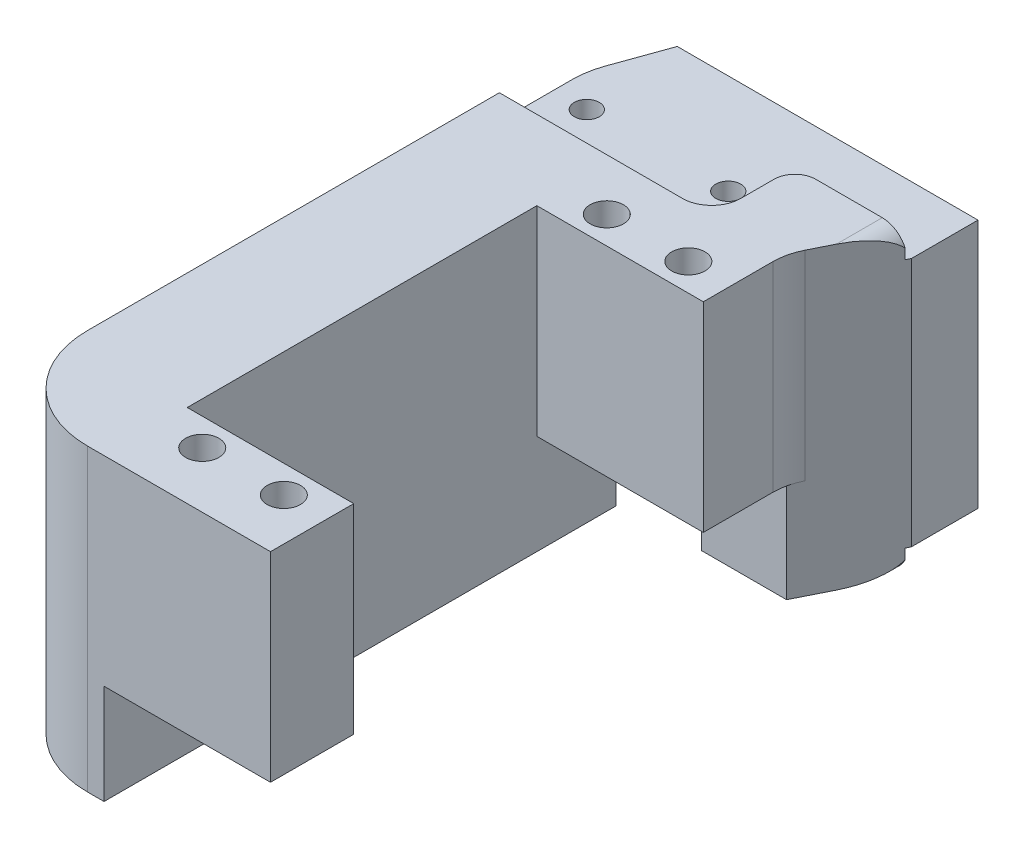
SolidWorks part; units mm, degrees
ref_plane "Front Plane" through (0, 0, 0) normal (0, 0, 1) x (1, 0, 0)
ref_plane "Top Plane" through (0, 0, 0) normal (0, 1, 0) x (1, 0, 0)
ref_plane "Right Plane" through (0, 0, 0) normal (1, 0, 0) x (0, 0, -1)
sketch "Sketch1" plane through (0, 33.4967, 0) normal (0, -1, 0) x (1, 0, 0)
  line L1 (-28.5725, 54.3439) -> (-28.5725, 64.3439)
  line L5 (-28.5725, -17.6561) -> (-28.5725, -7.6561) construction
  line L6 (-28.5725, -15.6561) -> (-64.703, -15.6561)
  line L7 (-53.5725, 54.3439) -> (-28.5725, 54.3439)
  line L8 (-28.5725, -69.4456) -> (-58.5726, -69.4456) construction
  line L9 (-28.5725, -17.6561) -> (-28.5725, -167.6561) construction
  line L10 (-58.5726, -37.091) -> (-58.5726, -177.6561) construction
  line L11 (-43.5725, -69.4456) -> (-43.5725, 6.1239) construction
  line L12 (-66.9858, -9.2936) -> (-60.0414, -28.6479) construction
  line L13 (-66.9858, -9.2936) -> (-64.703, -15.6561)
  line L14 (-28.5725, 64.3439) -> (-67.5734, 64.3439)
  line L16 (-28.5725, -15.6561) -> (-28.5725, 12.3439)
  line L22 (-67.5734, -5.9164) -> (-67.5734, 64.3439)
  line L23 (-51.5725, 6.1239) -> (-35.5725, 6.1239) construction
  line L24 (-60.6501, 64.3439) -> (-60.6501, 2.3439) construction
  line L25 (-67.5734, 2.3439) -> (-45.5734, 2.3439) construction
  line L26 (-60.6501, 33.3439) -> (-17.0153, 33.3439) construction
  line L27 (-53.5725, 54.3439) -> (-53.5725, 12.3439)
  line L28 (-53.5725, 12.3439) -> (-28.5725, 12.3439)
  arc A0 (-67.5734, -5.9164) -> (-66.9858, -9.2936) centre (-57.5734, -5.9164) ccw construction
  arc A1 (-67.5734, -5.9164) -> (-66.9858, -9.2936) centre (-57.5734, -5.9164) ccw
  circle A4 centre (-46.5734, -3.6561) radius 2.1 construction
  dimension "D2" = 12
  dimension "D1" = 80
  dimension "D3" = 10
  dimension "D4" = 42
  dimension "D5" = 21
extrude "Boss-Extrude1" add sketch "Sketch1" along normal up to vertex (26 mm away)
sketch "Sketch3" plane through (0, -2.5033, 0) normal (0, -1, 0) x (1, 0, 0)
  line L8 (-28.5725, -15.6561) -> (-67.5734, -15.6561)
  line L9 (-67.5734, -196.5548) -> (-67.5734, -11.5548) construction
  line L11 (-28.5725, -7.1561) -> (-39.5734, -7.1561)
  line L12 (-42.0734, -0.6561) -> (-42.0734, -4.6561)
  line L13 (-67.5734, 2.8439) -> (-45.5734, 2.8439)
  line L14 (-28.5725, -7.1561) -> (-28.5725, -15.6561)
  line L15 (-67.5734, 2.8439) -> (-67.5734, -15.6561)
  arc A3 (-42.0734, -4.6561) -> (-39.5734, -7.1561) centre (-39.5734, -4.6561) ccw
  arc A4 (-45.5734, 2.8439) -> (-42.0734, -0.6561) centre (-45.5734, -0.6561) cw
extrude "Cut-Extrude2" cut sketch "Sketch3" against normal blind 3
sketch "Sketch4" plane through (0, 33.4967, 0) normal (0, 1, 0) x (1, 0, 0)
  line L6 (-67.5734, 15.6561) -> (-67.5734, -2.8439)
  line L7 (-67.5734, 15.6561) -> (-67.5734, -2.8439)
  line L8 (-67.5734, -2.8439) -> (-45.5734, -2.8439)
  line L9 (-28.5725, 15.6561) -> (-67.5734, 15.6561)
  line L10 (-67.5734, -2.8439) -> (-45.5734, -2.8439)
  line L11 (-42.0734, 0.6561) -> (-42.0734, 4.6561)
  line L15 (-28.5725, 15.6561) -> (-67.5734, 15.6561)
  line L18 (-42.0734, 0.6561) -> (-42.0734, 4.6561)
  line L19 (-39.5734, 7.1561) -> (-28.5725, 7.1561)
  line L20 (-39.5734, 7.1561) -> (-28.5725, 7.1561)
  line L21 (-28.5725, 7.1561) -> (-28.5725, 15.6561)
  line L22 (-28.5725, 7.1561) -> (-28.5725, 15.6561)
  arc A2 (-45.5734, -2.8439) -> (-42.0734, 0.6561) centre (-45.5734, 0.6561) ccw
  arc A3 (-45.5734, -2.8439) -> (-42.0734, 0.6561) centre (-45.5734, 0.6561) ccw
  arc A6 (-39.5734, 7.1561) -> (-42.0734, 4.6561) centre (-39.5734, 4.6561) ccw
  arc A7 (-39.5734, 7.1561) -> (-42.0734, 4.6561) centre (-39.5734, 4.6561) ccw
  dimension "D1" = 0
extrude "Cut-Extrude3" cut sketch "Sketch4" against normal blind 3
fillet "Fillet3" radius 12
sketch "Sketch5" plane through (0, -2.5033, 0) normal (0, -1, 0) x (1, 0, 0)
  line L0 (-28.5725, -7.1561) -> (-28.5725, 12.3439) construction
  line L1 (-53.5725, 12.3439) -> (-28.5725, 12.3439)
  line L2 (-53.5725, 12.3439) -> (-53.5725, 2.3439)
  line L3 (-53.5725, 2.3439) -> (-28.5725, 2.3439)
  line L4 (-28.5725, 12.3439) -> (-28.5725, 2.3439)
  line L6 (-28.5725, 64.3439) -> (-53.5725, 64.3439)
  line L7 (-28.5725, 64.3439) -> (-28.5725, 54.3439)
  line L8 (-28.5725, 54.3439) -> (-53.5725, 54.3439)
  line L9 (-53.5725, 64.3439) -> (-53.5725, 54.3439)
  line L10 (-53.5725, 54.3439) -> (-28.5725, 54.3439) construction
  dimension "D1" = 0
  dimension "D2" = 0
  dimension "D3" = 10
extrude "Cut-Extrude4" cut sketch "Sketch5" against normal blind 12
sketch "Sketch6" plane through (0, 9.4967, 0) normal (0, -1, 0) x (1, 0, 0)
  line L0 (-33.5725, 64.3439) -> (-33.5725, 2.3439)
  line L2 (-43.7706, 2.3439) -> (-28.5725, 2.3439) construction
  line L3 (-33.5725, 2.3439) -> (-28.5725, -7.6561)
  line L4 (-28.5725, -7.6561) -> (-28.5725, 64.3439)
  line L5 (-28.5725, 64.3439) -> (-33.5725, 64.3439)
extrude "Cut-Extrude5" cut sketch "Sketch6" against normal through all both and the other way through all
fillet "Fillet4" radius 7
sketch "Sketch7" plane through (0, 0, -15.6561) normal (0, 0, -1) x (-1, 0, 0)
  line L0 (31.5725, -2.5033) -> (28.5725, -2.5033)
  line L1 (28.5725, -2.5033) -> (28.5725, 0.4967)
  line L2 (31.5725, 33.4967) -> (28.5725, 33.4967)
  line L3 (28.5725, 33.4967) -> (28.5725, 30.4967)
  arc A0 (28.5725, 0.4967) -> (31.5725, -2.5033) centre (31.5725, 0.4967) ccw construction
  arc A1 (28.5725, 0.4967) -> (31.5725, -2.5033) centre (31.5725, 0.4967) ccw
  arc A2 (31.5725, 33.4967) -> (28.5725, 30.4967) centre (31.5725, 30.4967) ccw construction
  arc A3 (31.5725, 33.4967) -> (28.5725, 30.4967) centre (31.5725, 30.4967) ccw
extrude "Cut-Extrude6" cut sketch "Sketch7" against normal through all both
sketch "Sketch8" plane through (0, 0.4967, 0) normal (0, -1, 0) x (1, 0, 0)
  circle A0 centre (-46.5734, -3.6561) radius 1.5
  circle A1 centre (-63.5734, -3.6561) radius 1.5
  circle A2 centre (-38.6725, 9.0439) radius 2
  circle A3 centre (-48.4725, 9.0439) radius 2
  circle A4 centre (-48.4725, 57.6439) radius 2
  circle A5 centre (-38.6725, 57.6439) radius 2
extrude "Cut-Extrude7" cut sketch "Sketch8" against normal through all
